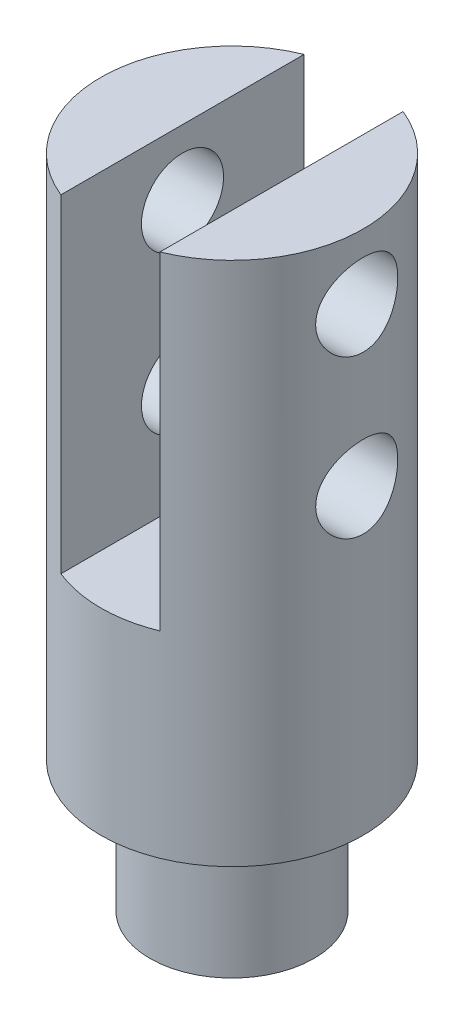
SolidWorks part; units mm, degrees
ref_plane "Front Plane" through (0, 0, 0) normal (0, 0, 1) x (1, 0, 0)
ref_plane "Top Plane" through (0, 0, 0) normal (0, 1, 0) x (1, 0, 0)
ref_plane "Right Plane" through (0, 0, 0) normal (1, 0, 0) x (0, 0, -1)
sketch "Sketch1" plane through (0, 0, 0) normal (1, 0, 0) x (0, 0, -1)
  line L0 (0, 0) -> (-12.7, 0)
  line L1 (-12.7, 0) -> (-12.7, -50.8)
  line L5 (0, -50.8) -> (0, 0)
  line L6 (0, 54.1051) -> (0, -152.4) construction
  line L12 (-12.7, -50.8) -> (-7.9375, -50.8)
  line L13 (-7.9375, -50.8) -> (-7.9375, -63.5)
  line L14 (-7.9375, -63.5) -> (0, -63.5)
  line L15 (0, -63.5) -> (0, -50.8)
  dimension "D1" = 50.8
  dimension "D2" = 15.875
  dimension "D3" = 12.7
  dimension "D7" = 25.4
revolve "Revolve1" add sketch "Sketch1" angle 360 about L6
sketch "Sketch2" plane through (0, 0, 0) normal (0, 1, 0) x (1, 0, 0)
  line L0 (-2.54, 5.08) -> (2.54, 5.08)
  line L1 (2.54, 2.54) -> (2.54, -2.54)
  line L2 (2.54, -5.08) -> (-2.54, -5.08)
  line L3 (-2.54, -2.54) -> (-2.54, 2.54)
  arc A0 (-2.54, 5.08) -> (-2.54, 2.54) centre (-2.54, 3.81) ccw
  arc A1 (2.54, 2.54) -> (2.54, 5.08) centre (2.54, 3.81) ccw
  arc A2 (2.54, -5.08) -> (2.54, -2.54) centre (2.54, -3.81) ccw
  arc A3 (-2.54, -2.54) -> (-2.54, -5.08) centre (-2.54, -3.81) ccw
  point P3 (-2.54, 0)
  point P5 (0, 5.08)
  dimension "D3" = 2.54
  dimension "D4" = 2.54
  dimension "D5" = 2.54
  dimension "D6" = 2.54
  dimension "D1" = 5.08
  dimension "D2" = 10.16
extrude "Cut-Extrude1" [suppressed] cut sketch "Sketch2" against normal blind 10.16
sketch "Sketch3" plane through (0, 0, 0) normal (0, 1, 0) x (1, 0, 0)
  line L1 (-4.7879, -26.2227) -> (4.7879, -26.2227)
  line L2 (-4.7879, -26.2227) -> (-4.7879, 26.2227)
  line L3 (-4.7879, 26.2227) -> (4.7879, 26.2227)
  line L4 (4.7879, -26.2227) -> (4.7879, 26.2227)
  line L5 (-4.7879, -26.2227) -> (4.7879, 26.2227) construction
  line L6 (-4.7879, 26.2227) -> (4.7879, -26.2227) construction
  point P0 (0, 0)
  dimension "D1" = 9.5758
extrude "Cut-Extrude2" cut sketch "Sketch3" against normal blind 31.75
ref_plane "Plane1" through (12.7, 0, 0) normal (1, 0, 0) x (0, 0, -1)
sketch "Sketch4" plane through (12.7, 0, 0) normal (1, 0, 0) x (0, 0, -1)
  circle A0 centre (0, -6.35) radius 3.9726
  circle A1 centre (0, -21.59) radius 3.9688
  dimension "D1" = 7.9451
  dimension "D3" = 15.24
  dimension "D2" = 6.35
extrude "Cut-Extrude3" cut sketch "Sketch4" against normal through all
ref_plane "Plane2" through (-12.7, 0, 0) normal (-1, 0, 0) x (0, 0, 1)
